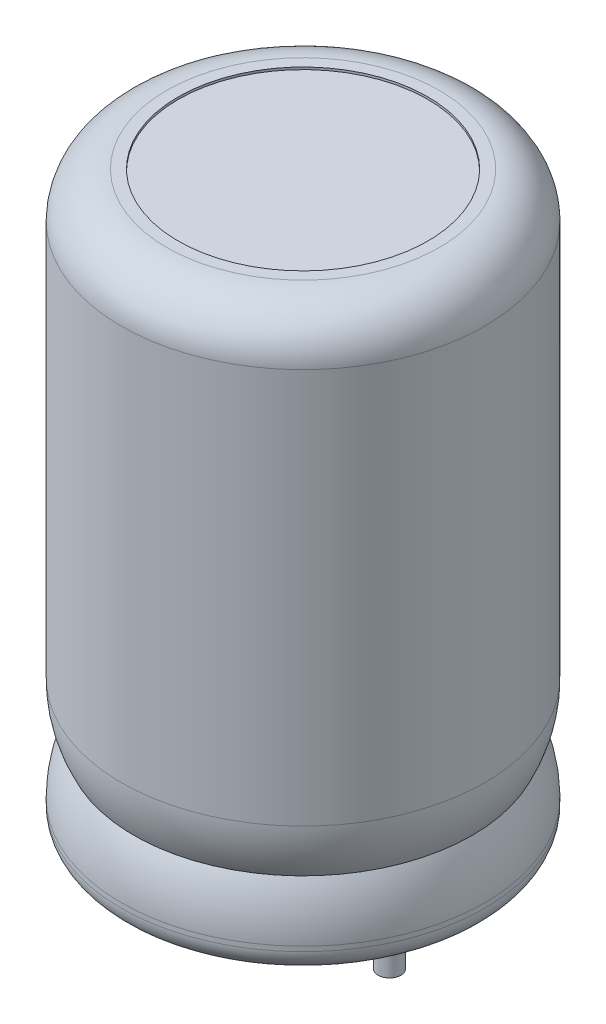
SolidWorks part; units mm, degrees
ref_plane "Front Plane" through (0, 0, 0) normal (0, 0, 1) x (1, 0, 0)
ref_plane "Top Plane" through (0, 0, 0) normal (0, 1, 0) x (1, 0, 0)
ref_plane "Right Plane" through (0, 0, 0) normal (1, 0, 0) x (0, 0, -1)
sketch "Sketch1" plane through (0, 0, 0) normal (0, 0, 1) x (1, 0, 0)
  line L0 (-3.81, 25.2) -> (-3.81, 0) construction
  line L1 (-3.81, 0.1) -> (1.69, 0.1)
  line L2 (1.69, 25.2) -> (2.19, 25.2)
  line L3 (1.69, 0.1) -> (1.69, 0)
  line L4 (1.69, 0) -> (3.19, 0)
  line L5 (4.19, 23.2) -> (4.19, 5.79)
  line L6 (4.19, 1.21) -> (4.19, 1)
  line L7 (-3.81, 25.1) -> (-3.81, 0.1)
  line L8 (-3.81, 25.1) -> (1.69, 25.1)
  line L9 (1.69, 25.1) -> (1.69, 25.2)
  arc A0 (2.19, 25.2) -> (4.19, 23.2) centre (2.19, 23.2) cw
  arc A3 (3.19, 0) -> (4.19, 1) centre (3.19, 1) ccw
  arc A4 (4.19, 1.21) -> (3.6348, 3.5) centre (-0.81, 1.21) ccw
  arc A5 (3.6348, 3.5) -> (4.19, 5.79) centre (-0.81, 5.79) ccw
  point P9 (4.19, 25.2)
  point P18 (4.19, 0)
  dimension "D4" = 2
  dimension "D5" = 4.58
  dimension "D7" = 5
  dimension "D1" = 1
  dimension "D2" = 8
  dimension "D3" = 25.2
  dimension "D6" = 0.21
  dimension "D8" = 5.5
  dimension "D9" = 0.1
  dimension "D10" = 3.81
  dimension "D11" = 5.5
  dimension "D12" = 0.1
revolve "Base-Revolve" add sketch "Sketch1" angle 360 about L0
sketch "Sketch2" plane through (0, 0.1, 0) normal (0, -1, 0) x (1, 0, 0)
  line L0 (0, 0) -> (-18.087, 0) construction
  circle A0 centre (0, 0) radius 0.5
  circle A1 centre (-7.62, 0) radius 0.5
  circle A2 centre (-3.81, 0) radius 5.5 construction
  circle A3 centre (-3.81, 0) radius 3.81 construction
  point P6 (-3.81, 0)
  dimension "D1" = 1
extrude "Boss-Extrude1" add sketch "Sketch2" along normal blind 3.5
ref_plane "Board Plane" through (0, -0.5, 0) normal (0, 1, 0) x (-1, 0, 0)
sketch "Component_Outline" plane through (0, -0.5, 0) normal (0, 1, 0) x (-1, 0, 0)
  circle A0 centre (3.81, 0) radius 8
  circle A3 centre (3.81, 0) radius 8 construction
  point P4 (0, 0)
